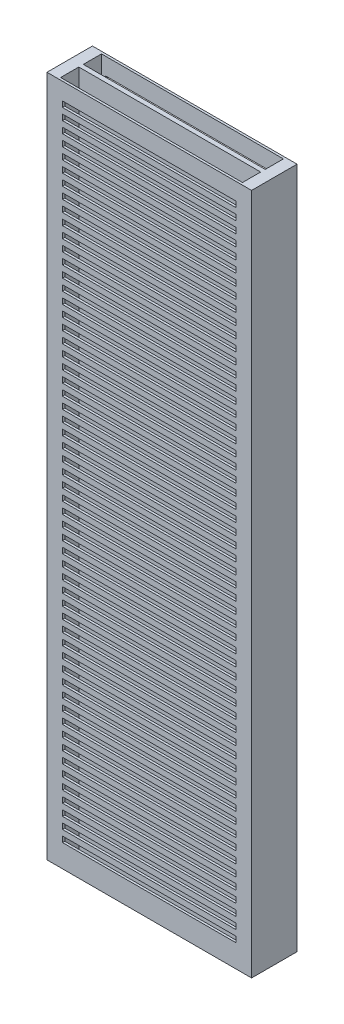
SolidWorks part; units mm, degrees
ref_plane "Front Plane" through (0, 0, 0) normal (0, 0, 1) x (1, 0, 0)
ref_plane "Top Plane" through (0, 0, 0) normal (0, 1, 0) x (1, 0, 0)
ref_plane "Right Plane" through (0, 0, 0) normal (1, 0, 0) x (0, 0, -1)
sketch "Sketch1" plane through (0, 0, 0) normal (0, 1, 0) x (1, 0, 0)
  line L1 (-4.5, -1) -> (4.5, -1)
  line L2 (-4.5, -1) -> (-4.5, 1)
  line L3 (-4.5, 1) -> (4.5, 1)
  line L4 (4.5, -1) -> (4.5, 1)
  line L5 (-4.5, -1) -> (4.5, 1) construction
  line L6 (-4.5, 1) -> (4.5, -1) construction
  point P0 (0, 0)
  dimension "D1" = 9
  dimension "D2" = 2
extrude "Boss-Extrude1" add sketch "Sketch1" along normal mid plane 30
sketch "Sketch2" plane through (0, 15, 0) normal (0, 1, 0) x (1, 0, 0)
  line L1 (-4, 0.1) -> (4, 0.1)
  line L2 (-4, 0.1) -> (-4, 0.9)
  line L3 (-4, 0.9) -> (4, 0.9)
  line L4 (4, 0.1) -> (4, 0.9)
  line L5 (-4, 0.1) -> (4, 0.9) construction
  line L6 (-4, 0.9) -> (4, 0.1) construction
  point P0 (0, 0.5)
  dimension "D1" = 0.8
  dimension "D2" = 8
  dimension "D3" = 0
  dimension "D4" = 0.5
extrude "Cut-Extrude1" cut sketch "Sketch2" against normal through all and the other way through all
mirror "Mirror1" about plane through (0, 0, 0) normal (0, 0, 1) of "Cut-Extrude1"
sketch "Sketch3" plane through (0, 0, 1) normal (0, 0, 1) x (1, 0, 0)
  line L0 (0, -1.1) -> (0, 1.1) construction
  line L1 (-3.8171, 14) -> (3.8171, 14)
  line L2 (-3.8171, 14) -> (-3.8171, 14.25)
  line L3 (-3.8171, 14.25) -> (3.8171, 14.25)
  line L4 (3.8171, 14) -> (3.8171, 14.25)
  line L5 (-3.8171, 14) -> (3.8171, 14.25) construction
  line L6 (-3.8171, 14.25) -> (3.8171, 14) construction
  line L7 (-4.5, 15) -> (4.5, 15) construction
  point P0 (0, 14.125)
  dimension "D1" = 0.25
  dimension "D2" = 0.75
extrude "Cut-Extrude2" cut sketch "Sketch3" against normal up to next (0.1 mm away)
pattern_linear "LPattern1" count 57 spacing 0.5 along (0, -1, 0) of "Cut-Extrude2"
mirror "Mirror2" about plane through (0, 0, 0) normal (0, 0, 1) of "LPattern1", "Cut-Extrude2"
